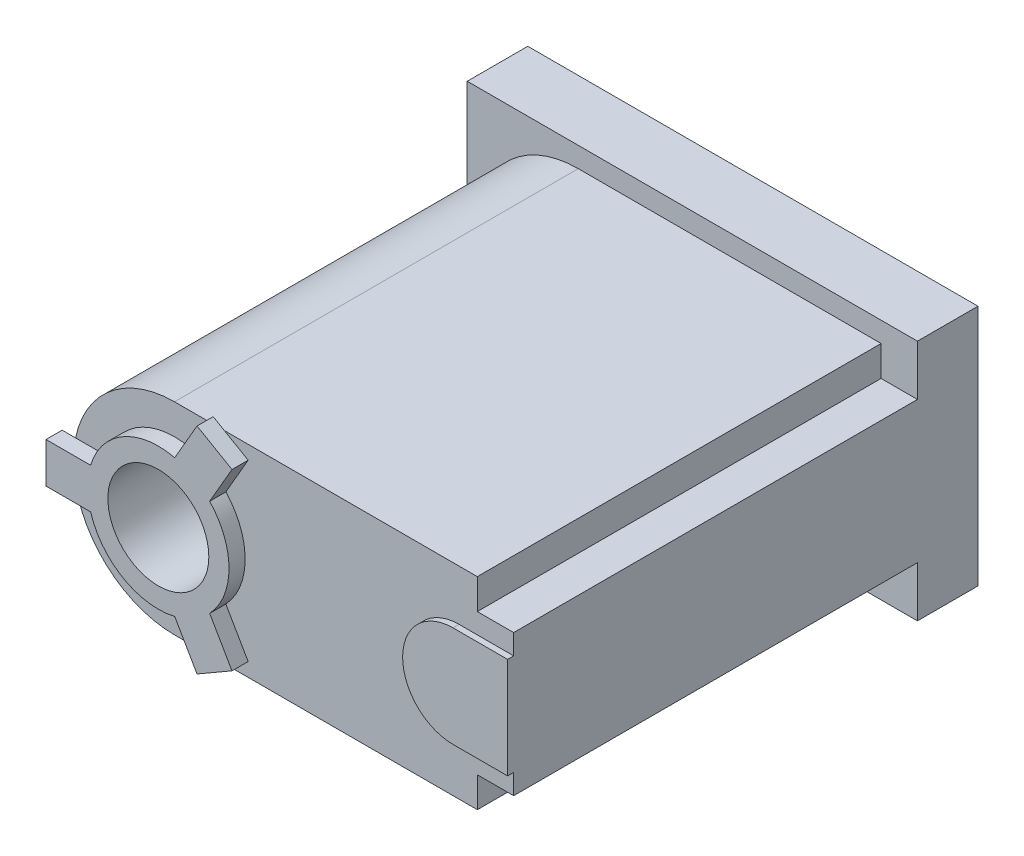
SolidWorks part; units mm, degrees
ref_plane "前视基准面" through (0, 0, 0) normal (0, 0, 1) x (1, 0, 0)
ref_plane "上视基准面" through (0, 0, 0) normal (0, 1, 0) x (1, 0, 0)
ref_plane "右视基准面" through (0, 0, 0) normal (1, 0, 0) x (0, 0, -1)
sketch "草图1" plane through (0, 0, 0) normal (0, 0, 1) x (1, 0, 0)
  line L0 (0, 50) -> (150, 50)
  line L1 (150, 50) -> (150, -50)
  line L2 (150, -50) -> (0, -50)
  circle A0 centre (0, 0) radius 25
  arc A1 (0, 50) -> (0, -50) centre (0, 0) ccw
extrude "凸台-拉伸1" add sketch "草图1" along normal blind 230
sketch "草图2" plane through (150, 0, 0) normal (1, 0, 0) x (0, 0, -1)
  line L0 (0, -35) -> (0, 35)
  line L1 (0, -50) -> (0, 50) construction
  line L2 (0, 35) -> (-230, 35)
  line L3 (-230, -50) -> (-230, 50) construction
  line L4 (-230, 35) -> (-230, -35)
  line L5 (-230, -35) -> (0, -35)
  dimension "D1" = 15
  dimension "D2" = 15
extrude "凸台-拉伸2" add sketch "草图2" along normal blind 18
sketch "草图3" plane through (0, 0, 0) normal (0, 0, -1) x (-1, 0, 0)
  line L0 (-168, -60) -> (-168, 60)
  line L1 (-168, 60) -> (55, 60)
  line L2 (55, 60) -> (55, -60)
  line L3 (55, -60) -> (-168, -60)
  line L4 (-150, 50) -> (0, 50) construction
  line L5 (0, -50) -> (-150, -50) construction
  arc A0 (0, -50) -> (0, 50) centre (0, 0) ccw construction
  point P9 (50, 0)
  dimension "D1" = 10
  dimension "D2" = 10
  dimension "D3" = 5
extrude "凸台-拉伸3" add sketch "草图3" against normal blind 30
sketch "草图4" plane through (0, 0, 230) normal (0, 0, 1) x (1, 0, 0)
  line L0 (168, 35) -> (168, -35) construction
  line L1 (168, 25) -> (141, 25)
  line L2 (168, 25) -> (168, -25)
  line L3 (168, -25) -> (141, -25)
  line L5 (168, 35) -> (150, 35) construction
  line L6 (168, -35) -> (150, -35) construction
  arc A0 (141, 25) -> (141, -25) centre (141, 0) ccw
  dimension "D1" = 10
  dimension "D2" = 10
extrude "凸台-拉伸4" add sketch "草图4" along normal blind 3
sketch "草图5" plane through (0, 0, 230) normal (0, 0, 1) x (1, 0, 0)
  line L0 (-55.6464, 10) -> (-55.6464, -10)
  line L1 (-55.6464, 10) -> (-33.541, 10)
  line L2 (19.1629, 53.1912) -> (8.1103, 34.0474)
  line L3 (-55.6464, -10) -> (-33.541, -10)
  line L4 (36.4834, 43.1912) -> (19.1629, 53.1912)
  line L5 (36.4834, 43.1912) -> (25.4308, 24.0474)
  line L6 (36.4834, -43.1912) -> (25.4308, -24.0474)
  line L7 (19.1629, -53.1912) -> (36.4834, -43.1912)
  line L8 (19.1629, -53.1912) -> (8.1103, -34.0474)
  circle A0 centre (0, 0) radius 25
  arc A1 (-33.541, -10) -> (8.1103, -34.0474) centre (0, 0) ccw
  arc A2 (0, 50) -> (0, -50) centre (0, 0) ccw construction
  arc A3 (8.1103, 34.0474) -> (-33.541, 10) centre (0, 0) ccw
  arc A4 (25.4308, -24.0474) -> (25.4308, 24.0474) centre (0, 0) ccw
  point P4 (-50, 0)
  dimension "D1" = 3
extrude "凸台-拉伸5" add sketch "草图5" along normal blind 8
